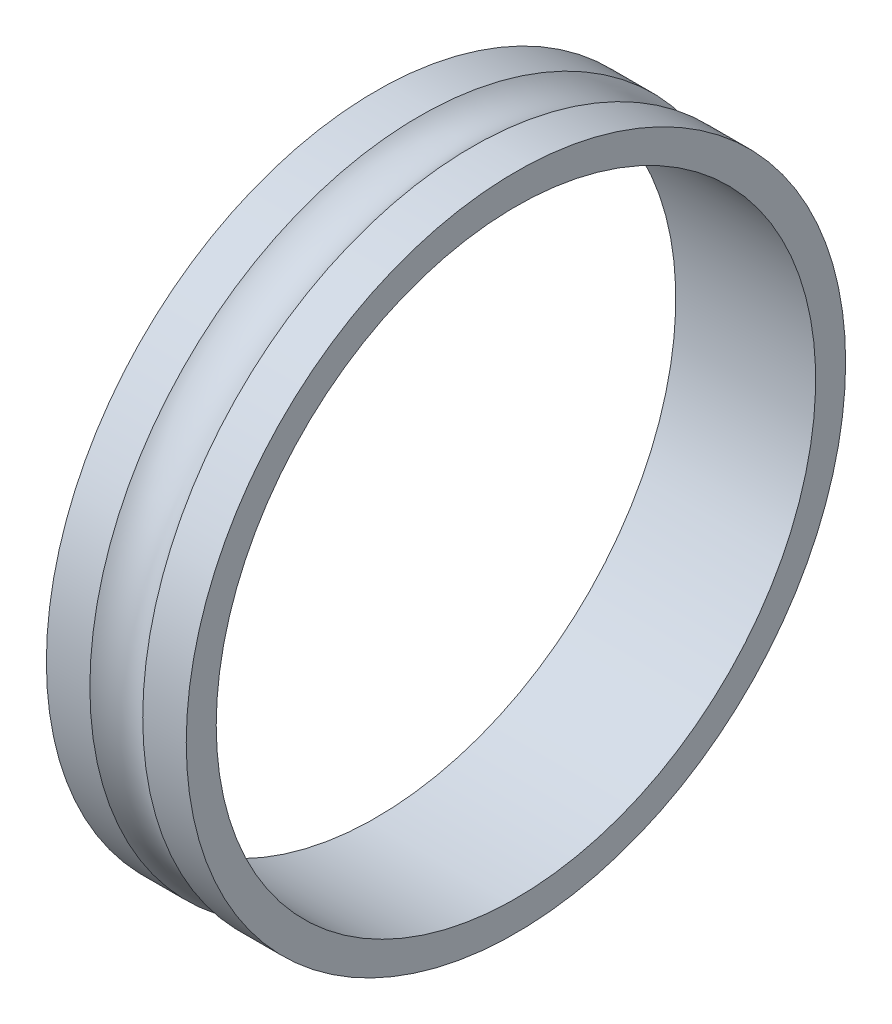
SolidWorks part; units mm, degrees
ref_plane "前视基准面" through (0, 0, 0) normal (0, 0, 1) x (1, 0, 0)
ref_plane "上视基准面" through (0, 0, 0) normal (0, 1, 0) x (1, 0, 0)
ref_plane "右视基准面" through (0, 0, 0) normal (1, 0, 0) x (0, 0, -1)
sketch "草图1" plane through (0, 0, 0) normal (0, 1, 0) x (1, 0, 0)
  line L0 (1.3229, 1.5) -> (3.5, 1.5)
  line L1 (-3.5, 3) -> (3.5, 3)
  line L2 (-3.5, 3) -> (-3.5, 1.5)
  line L4 (3.5, 3) -> (3.5, 1.5)
  line L5 (0, 3) -> (0, 18) construction
  line L6 (0, 18) -> (9.5401, 18) construction
  line L7 (-3.5, 1.5) -> (-1.3229, 1.5)
  arc A0 (1.3229, 1.5) -> (-1.3229, 1.5) centre (0, 0) ccw
  point P0 (0, 0)
  dimension "D3" = 4
  dimension "D1" = 7
  dimension "D2" = 15
  dimension "D5" = 1.5
revolve "旋转1" add sketch "草图1" angle 360 about L6
